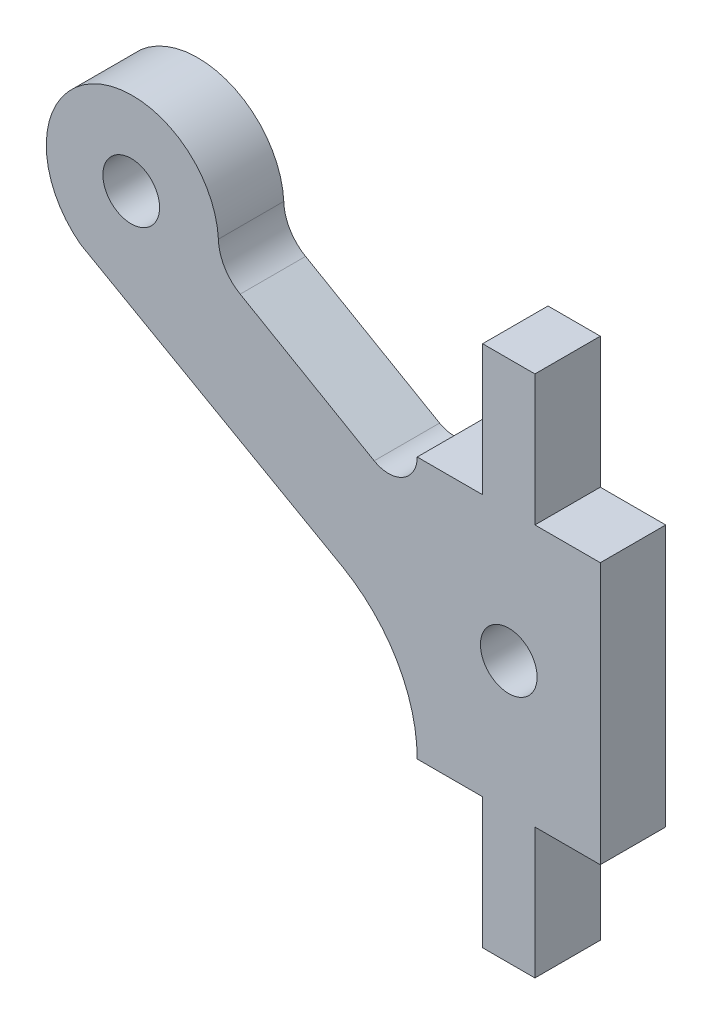
SolidWorks part; units mm, degrees
ref_plane "Front Plane" through (0, 0, 0) normal (0, 0, 1) x (1, 0, 0)
ref_plane "Top Plane" through (0, 0, 0) normal (0, 1, 0) x (1, 0, 0)
ref_plane "Right Plane" through (0, 0, 0) normal (1, 0, 0) x (0, 0, -1)
sketch "Model" plane through (0, 0, 0) normal (0, 0, 1) x (1, 0, 0)
  line L0 (74.2314, 47.6131) -> (74.2314, 35.6131)
  line L1 (71.2314, 35.6131) -> (74.2314, 35.6131)
  line L2 (71.2314, 29.6131) -> (71.2314, 35.6131)
  line L3 (68.8314, 29.6131) -> (71.2314, 29.6131)
  line L4 (68.8314, 35.6129) -> (68.8314, 29.6131)
  line L5 (65.8314, 35.6129) -> (68.8314, 35.6129)
  line L6 (50.3936, 48.3334) -> (62.4144, 41.5323)
  line L7 (63.8572, 46.4729) -> (57.7102, 50.0224)
  line L8 (68.8314, 47.613) -> (65.8314, 47.613)
  line L9 (68.8314, 53.6131) -> (68.8314, 47.613)
  line L10 (71.2314, 53.6131) -> (68.8314, 53.6131)
  line L11 (71.2314, 47.6131) -> (71.2314, 53.6131)
  line L12 (74.2314, 47.6131) -> (71.2314, 47.6131)
  circle A0 centre (70.0318, 41.6127) radius 1.3
  circle A1 centre (52.712, 51.614) radius 1.3
  arc A2 (65.8314, 35.6129) -> (62.4144, 41.5323) centre (58.9968, 35.6136) ccw
  arc A3 (56.7109, 51.7077) -> (50.3936, 48.3334) centre (52.7658, 51.4928) ccw
  arc A4 (56.7109, 51.7077) -> (57.7102, 50.0224) centre (58.7104, 51.7544) ccw
  arc A5 (63.8572, 46.4729) -> (65.8314, 47.613) centre (64.5148, 47.6135) ccw
  dimension "D1" = 12
  dimension "D2" = 2.4
  dimension "D3" = 6
  dimension "D4" = 6
  dimension "D5" = 8.4
  dimension "D6" = 8.4
extrude "Boss-Extrude1" add sketch "Model" along normal blind 3 contours A5 L7 A4 A3 L6 A2 L5 L4 L3 L2 L1 L0 L12 L11 L10 L9 L8 A1 A0
